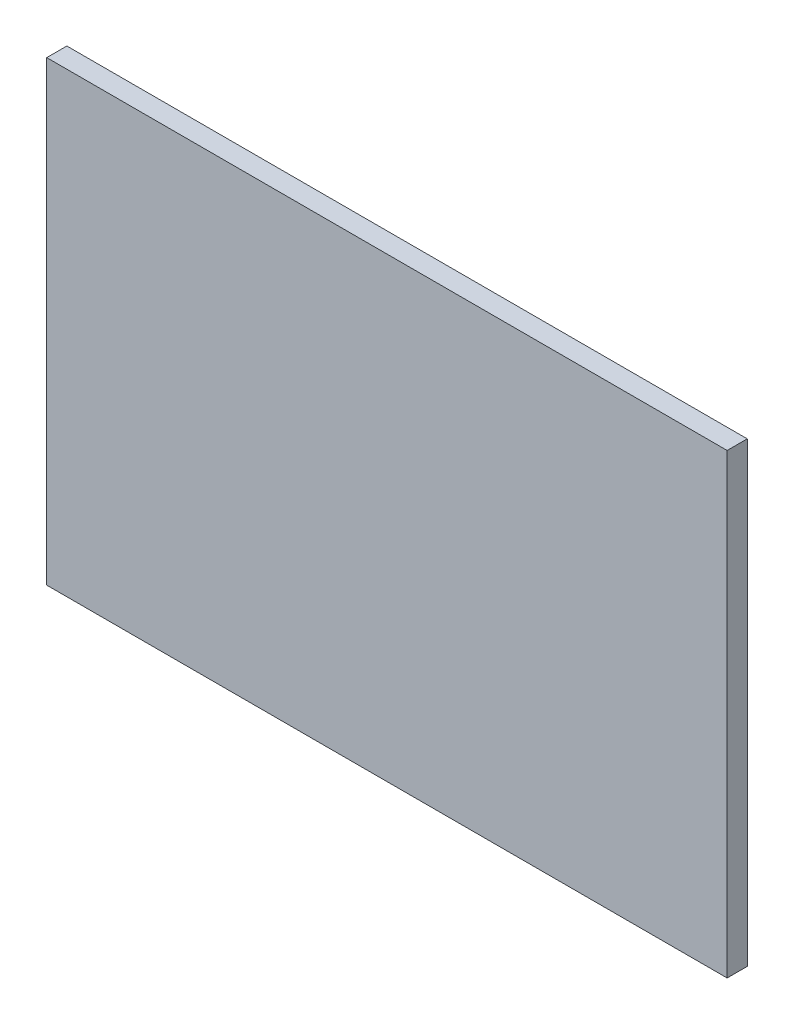
SolidWorks part; units mm, degrees
ref_plane "Plan de face" through (0, 0, 0) normal (0, 0, 1) x (1, 0, 0)
ref_plane "Plan de dessus" through (0, 0, 0) normal (0, 1, 0) x (1, 0, 0)
ref_plane "Plan de droite" through (0, 0, 0) normal (1, 0, 0) x (0, 0, -1)
sketch "Esquisse1" plane through (0, 0, 0) normal (0, 0, 1) x (1, 0, 0)
  line L1 (-1252.4272, 1339.8058) -> (1747.5728, 1339.8058)
  line L2 (-1252.4272, 1339.8058) -> (-1252.4272, -660.1942)
  line L3 (-1252.4272, -660.1942) -> (1747.5728, -660.1942)
  line L4 (1747.5728, 1339.8058) -> (1747.5728, -660.1942)
  dimension "D1" = 3000
  dimension "D2" = 2000
extrude "Boss.-Extru.1" add sketch "Esquisse1" along normal blind 20
sketch "Esquisse2" plane through (0, 0, 20) normal (0, 0, 1) x (1, 0, 0)
  line L4 (-1252.4272, 1339.8058) -> (-1252.4272, -660.1942)
  line L5 (-1252.4272, -660.1942) -> (1747.5728, -660.1942)
  line L6 (1747.5728, -660.1942) -> (1747.5728, 1339.8058)
  line L7 (1747.5728, 1339.8058) -> (-1252.4272, 1339.8058)
  line L8 (-1274.4272, 1361.8058) -> (-1274.4272, -682.1942)
  line L9 (-1274.4272, -682.1942) -> (1769.5728, -682.1942)
  line L10 (1769.5728, -682.1942) -> (1769.5728, 1361.8058)
  line L11 (1769.5728, 1361.8058) -> (-1274.4272, 1361.8058)
  line L12 (-1274.4272, 1361.8058) -> (-1274.4272, -682.1942)
  line L13 (-1274.4272, -682.1942) -> (1769.5728, -682.1942)
  line L14 (1769.5728, -682.1942) -> (1769.5728, 1361.8058)
  line L15 (1769.5728, 1361.8058) -> (-1274.4272, 1361.8058)
  dimension "D1" = 22
  dimension "D2" = 22
extrude "Boss.-Extru.2" add sketch "Esquisse2" against normal blind 90
sketch "Esquisse3" plane through (0, 0, 0) normal (0, 0, -1) x (-1, 0, 0)
  line L0 (-1747.5728, 1339.8058) -> (1252.4272, 1339.8058) construction
  line L1 (-1147.5728, 1339.8058) -> (652.4272, 1339.8058)
  line L2 (-1147.5728, 1339.8058) -> (-1147.5728, 889.8058)
  line L3 (-1147.5728, 889.8058) -> (652.4272, 889.8058)
  line L4 (652.4272, 1339.8058) -> (652.4272, 889.8058)
  line L5 (-1747.5728, -660.1942) -> (-1747.5728, 1339.8058) construction
  line L6 (1252.4272, 1339.8058) -> (1252.4272, -660.1942) construction
  dimension "D1" = 600
  dimension "D2" = 600
  dimension "D3" = 450
extrude "Boss.-Extru.3" add sketch "Esquisse3" along normal blind 55
sketch "Esquisse4" plane through (0, 0, -55) normal (0, 0, -1) x (-1, 0, 0)
  line L0 (-1147.5728, 1339.8058) -> (-1147.5728, 889.8058) construction
  line L1 (-1147.5728, 1339.8058) -> (-1132.5728, 1339.8058)
  line L2 (-1147.5728, 1339.8058) -> (-1147.5728, 889.8058)
  line L3 (-1147.5728, 889.8058) -> (-1132.5728, 889.8058)
  line L4 (-1132.5728, 1339.8058) -> (-1132.5728, 889.8058)
  line L5 (652.4272, 1339.8058) -> (-1147.5728, 1339.8058) construction
  line L6 (-1147.5728, 889.8058) -> (652.4272, 889.8058) construction
  line L7 (-1747.5728, 1339.8058) -> (1252.4272, 1339.8058) construction
  line L8 (652.4272, 889.8058) -> (637.4272, 889.8058)
  line L9 (652.4272, 889.8058) -> (652.4272, 1339.8058)
  line L10 (652.4272, 1339.8058) -> (637.4272, 1339.8058)
  line L11 (637.4272, 889.8058) -> (637.4272, 1339.8058)
  dimension "D1" = 15
  dimension "D2" = 15
extrude "Boss.-Extru.4" add sketch "Esquisse4" along normal blind 15
